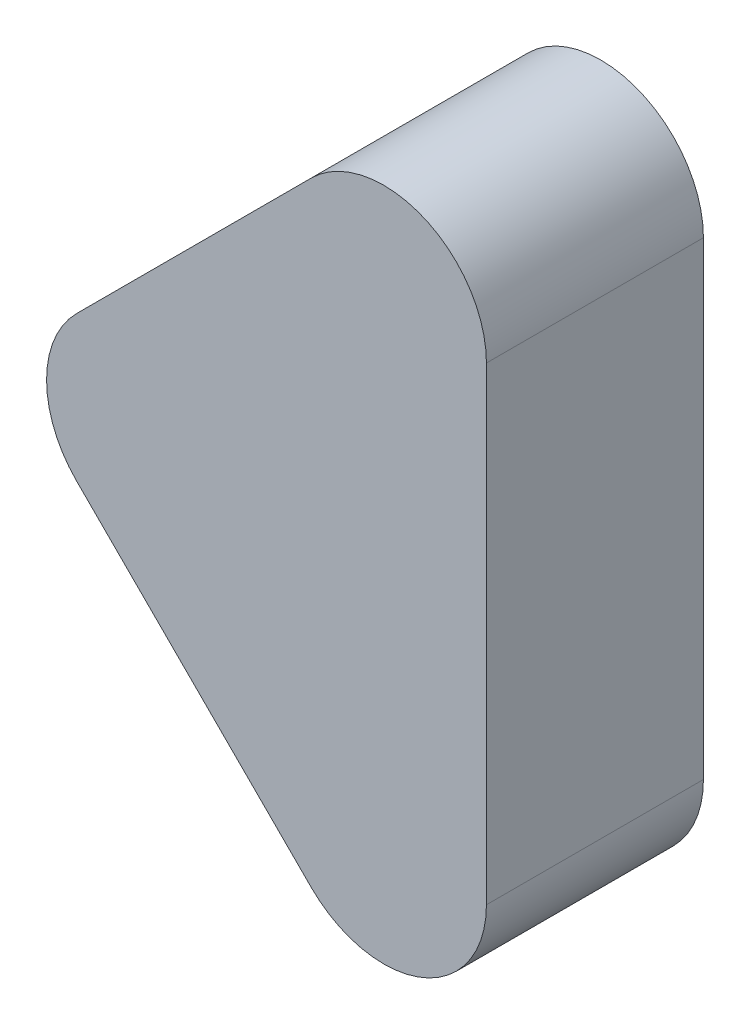
SolidWorks part; units mm, degrees
ref_plane "Front Plane" through (0, 0, 0) normal (0, 0, 1) x (1, 0, 0)
ref_plane "Top Plane" through (0, 0, 0) normal (0, 1, 0) x (1, 0, 0)
ref_plane "Right Plane" through (0, 0, 0) normal (1, 0, 0) x (0, 0, -1)
sketch "Sketch1" plane through (0, 0, 0) normal (0, 0, 1) x (1, 0, 0)
  line L6 (9.75, -19.725) -> (9.75, -11.725)
  line L7 (2.7626, -16.9624) -> (6.7626, -20.9624)
  line L8 (6.7626, -10.4876) -> (2.7626, -14.4876)
  line L9 (9.75, -19.725) -> (9.75, -11.725)
  line L10 (2.7626, -16.9624) -> (6.7626, -20.9624)
  line L11 (6.7626, -10.4876) -> (2.7626, -14.4876)
  arc A6 (9.75, -11.725) -> (6.7626, -10.4876) centre (8, -11.725) ccw
  arc A7 (6.7626, -20.9624) -> (9.75, -19.725) centre (8, -19.725) ccw
  arc A8 (2.7626, -14.4876) -> (2.7626, -16.9624) centre (4, -15.725) ccw
  arc A9 (9.75, -11.725) -> (6.7626, -10.4876) centre (8, -11.725) ccw
  arc A10 (6.7626, -20.9624) -> (9.75, -19.725) centre (8, -19.725) ccw
  arc A11 (2.7626, -14.4876) -> (2.7626, -16.9624) centre (4, -15.725) ccw
  dimension "D1" = 0.25
extrude "Boss-Extrude1" add sketch "Sketch1" along normal blind 3.7
sketch "Sketch2" plane through (0, 0, 3.7) normal (0, 0, 1) x (1, 0, 0)
  line L0 (9.75, -8.6661) -> (9.75, -24.3672) construction
  line L1 (4.7828, -21.475) -> (15.6259, -21.475) construction
  line L2 (9.75, -19.725) -> (9.75, -11.725) construction
  arc A0 (6.7626, -20.9624) -> (9.75, -19.725) centre (8, -19.725) ccw construction
  point P9 (9.75, -21.475)
